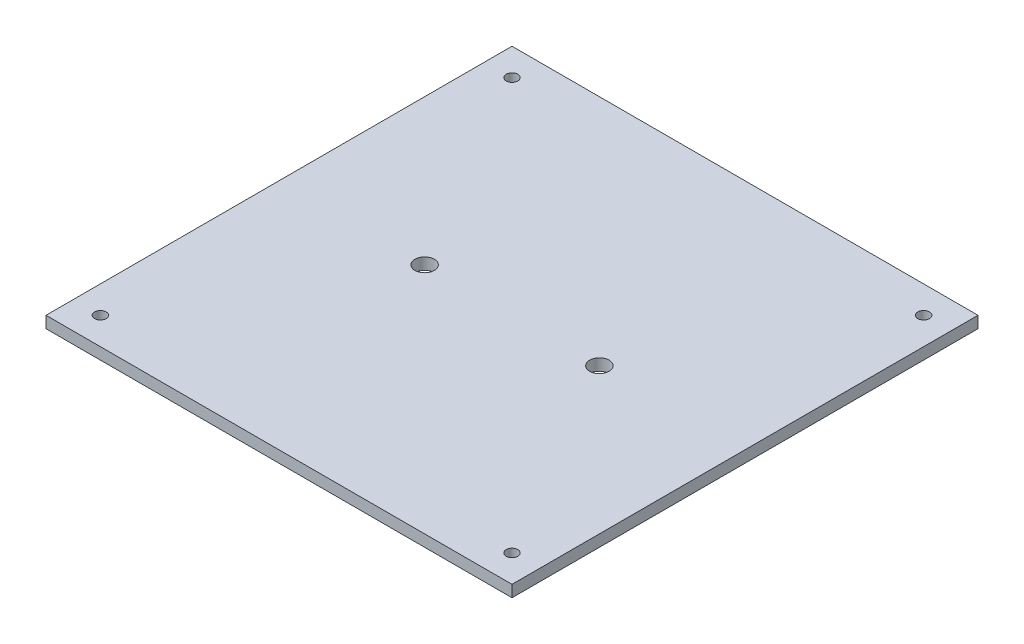
SolidWorks part; units mm, degrees
ref_plane "Front Plane" through (0, 0, 0) normal (0, 0, 1) x (1, 0, 0)
ref_plane "Top Plane" through (0, 0, 0) normal (0, 1, 0) x (1, 0, 0)
ref_plane "Right Plane" through (0, 0, 0) normal (1, 0, 0) x (0, 0, -1)
sketch "Sketch1" plane through (0, 0, 0) normal (0, 1, 0) x (1, 0, 0)
  line L1 (-60, -60) -> (60, -60)
  line L2 (-60, -60) -> (-60, 60)
  line L3 (-60, 60) -> (60, 60)
  line L4 (60, -60) -> (60, 60)
  line L5 (-60, -60) -> (60, 60) construction
  line L6 (-60, 60) -> (60, -60) construction
  point P0 (0, 0)
extrude "Boss-Extrude1" add sketch "Sketch1" along normal blind 3
sketch "Sketch2" plane through (0, 0, 0) normal (0, 1, 0) x (1, 0, 0)
  line L0 (-26, 0) -> (-26, 56.4247) construction
  line L1 (26, 0) -> (26, 58.8481) construction
  line L2 (0, 0) -> (0, 57.0064) construction
  line L3 (-19, 0) -> (-19, 37.3668) construction
  line L4 (19, 0) -> (19, 22.4016) construction
  line L5 (0, 0) -> (62.369, 0) construction
  line L6 (-22.5, 0) -> (-22.5, 36.1696) construction
  line L7 (22.5, 0) -> (22.5, 30.9816) construction
  dimension "D1" = 26
  dimension "D2" = 26
  dimension "D3" = 3.5
  dimension "D4" = 3.5
  dimension "D5" = 7
  dimension "D6" = 7
ref_point "Point1"
ref_point "Point2"
sketch "Sketch4" plane through (0, 0, 0) normal (0, 1, 0) x (1, 0, 0)
  circle A0 centre (-22.5, 0) radius 2.5
  circle A1 centre (22.5, 0) radius 2.5
extrude "Cut-Extrude2" cut sketch "Sketch4" along normal up to surface (3 mm away) up to face at (0, 3, 0)
sketch "Sketch5" plane through (0, 0, 0) normal (0, 1, 0) x (1, 0, 0)
  line L0 (-53, 0) -> (-53, 74.8856) construction
  line L1 (-55.2997, 53) -> (111.0551, 53) construction
  line L2 (53, 55.042) -> (53, 97.6787) construction
  line L3 (-55.2997, -53) -> (133.2261, -53) construction
  line L4 (-60, 60) -> (-60, -60) construction
  line L5 (60, -60) -> (60, 60) construction
  line L6 (-60, -60) -> (60, -60) construction
  line L7 (60, 60) -> (-60, 60) construction
  dimension "D1" = 7
  dimension "D2" = 7
  dimension "D3" = 7
  dimension "D4" = 7
ref_point "Point3"
ref_point "Point4"
ref_point "Point5"
ref_point "Point6"
sketch "Sketch7" plane through (0, 0, 0) normal (0, 1, 0) x (1, 0, 0)
  line L0 (-53, -200000) -> (-53, 200074.8856) construction
  line L1 (-200055.2997, -53) -> (200133.2261, -53) construction
  line L2 (53, -199944.958) -> (53, 200097.6787) construction
  circle A0 centre (-53, 53) radius 1.5
  circle A1 centre (53, 53) radius 1.5
  circle A2 centre (-53, -53) radius 1.5
  circle A3 centre (53, -53) radius 1.5
extrude "Cut-Extrude3" cut sketch "Sketch7" along normal up to surface (3 mm away) up to face at (-22.5, 3, -2.5)
